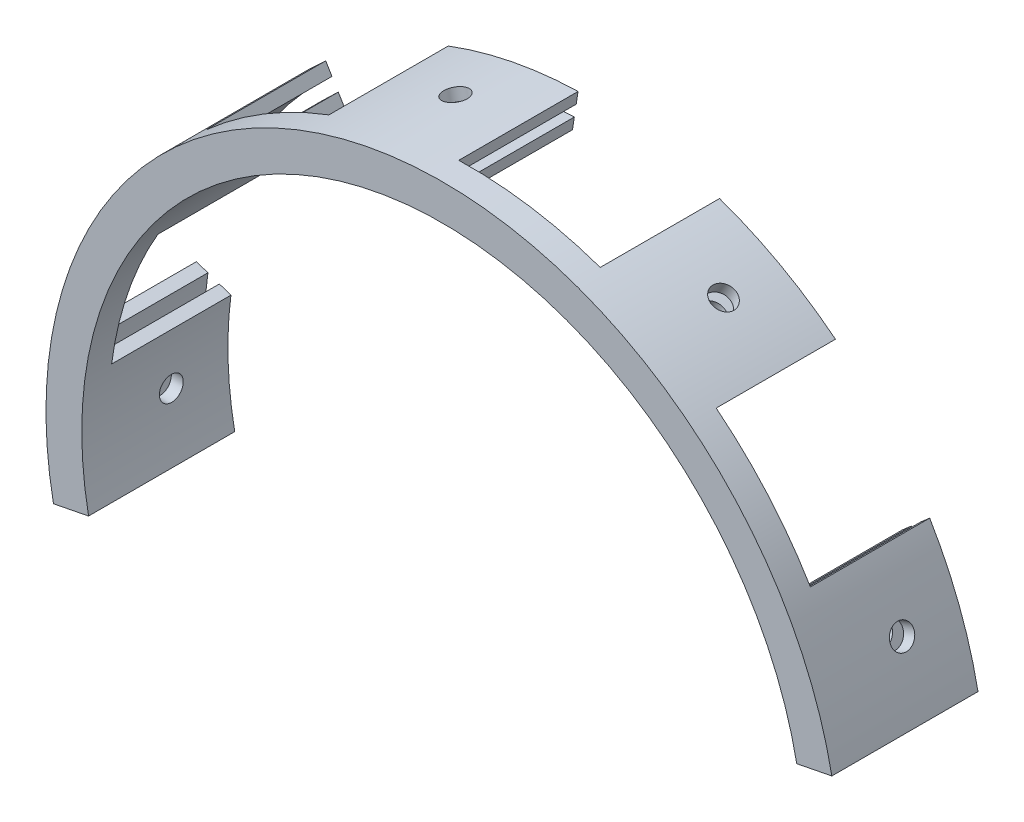
SolidWorks part; units mm, degrees
ref_plane "Front Plane" through (0, 0, 0) normal (0, 0, 1) x (1, 0, 0)
ref_plane "Top Plane" through (0, 0, 0) normal (0, 1, 0) x (1, 0, 0)
ref_plane "Right Plane" through (0, 0, 0) normal (1, 0, 0) x (0, 0, -1)
sketch "Sketch1" plane through (0, 0, 0) normal (0, 0, 1) x (1, 0, 0)
  line L2 (63.2821, 12.4748) -> (65.2444, 12.8616)
  line L3 (61.3199, 12.088) -> (59.3577, 11.7012)
  line L4 (-63.2821, -12.4748) -> (-61.3199, -12.088)
  line L5 (61.3199, 12.088) -> (63.2821, 12.4748)
  line L8 (-61.3199, -12.088) -> (-59.3577, -11.7012)
  line L9 (-63.2821, -12.4748) -> (-65.2444, -12.8616)
  arc A2 (65.2444, 12.8616) -> (-65.2444, -12.8616) centre (0, 0) ccw
  arc A3 (59.3577, 11.7012) -> (-59.3577, -11.7012) centre (0, 0) ccw
  arc A4 (63.2821, 12.4748) -> (-63.2821, -12.4748) centre (0, 0) ccw
  arc A5 (61.3199, 12.088) -> (-61.3199, -12.088) centre (0, 0) ccw
  arc A6 (63.2821, 12.4748) -> (-63.2821, -12.4748) centre (0, 0) ccw
  arc A7 (61.3199, 12.088) -> (-61.3199, -12.088) centre (0, 0) ccw
  dimension "D1" = 0
  dimension "D2" = 2
  dimension "D3" = 2
extrude "Boss-Extrude1" add sketch "Sketch1" against normal blind 22
sketch "Sketch2" plane through (0, 0, 0) normal (0, 0, 1) x (1, 0, 0)
  line L0 (-65.2444, -12.8616) -> (-59.3577, -11.7012)
  line L1 (59.3577, 11.7012) -> (65.2444, 12.8616)
  arc A0 (65.2444, 12.8616) -> (-65.2444, -12.8616) centre (0, 0) ccw construction
  arc A1 (59.3577, 11.7012) -> (-59.3577, -11.7012) centre (0, 0) ccw construction
  arc A2 (65.2444, 12.8616) -> (-65.2444, -12.8616) centre (0, 0) ccw
  arc A3 (59.3577, 11.7012) -> (-59.3577, -11.7012) centre (0, 0) ccw
extrude "Boss-Extrude2" add sketch "Sketch2" along normal blind 2.5
sketch "Sketch4" plane through (0, 0, 0) normal (0.1934, -0.9811, 0) x (0.9811, 0.1934, 0)
  line L0 (0, 0) -> (0, 49.5442) construction
  line L1 (0, 0) -> (24.6684, 0) construction
sketch "Sketch6" plane through (0, 0, 2.5) normal (0, 0, 1) x (1, 0, 0)
  line L0 (0, 0) -> (56.424, 21.8308) construction
  line L1 (0, 0) -> (59.3577, 11.7012) construction
  line L2 (0, 0) -> (45.5547, 39.8124) construction
  arc A0 (59.3577, 11.7012) -> (-59.3577, -11.7012) centre (0, 0) ccw construction
  point P6 (0, 0)
  dimension "D1" = 10
  dimension "D2" = 20
ref_plane "Plane3" through (56.424, 21.8308, 2.5) normal (0.9326, 0.3608, 0) x (0, 0, -1)
sketch "Sketch7" plane through (56.424, 21.8308, 2.5) normal (0.9326, 0.3608, 0) x (0, 0, -1)
  line L2 (0, 66.5) -> (0, -11.5476) construction
  line L3 (2.5, 0) -> (-47.0442, 0) construction
  line L4 (15, 0) -> (-47.0442, 0) construction
  circle A0 centre (15, 0) radius 2
  point P2 (13.5134, 0)
  point P5 (0, 0)
  point P8 (0, 0)
  point P9 (14.698, 0)
  dimension "D1" = 4
  dimension "D2" = 15
extrude "Cut-Extrude2" cut sketch "Sketch7" against normal through all both and the other way through all contours A0
pattern_circular "CirPattern1" count 5 every 40 about axis through (0, 0, 0) along (0, 0, 1) of "Cut-Extrude2"
ref_plane "Plane4" through (45.5547, 39.8124, 2.5) normal (0.753, 0.6581, 0) x (0, 0, -1)
sketch "Sketch8" plane through (45.5547, 39.8124, 2.5) normal (0.753, 0.6581, 0) x (0, 0, -1)
  line L0 (24.5, -33.25) -> (24.5, 66.5) construction
  line L1 (24.5, 12) -> (4.5, 12)
  line L2 (24.5, 12) -> (24.5, -12)
  line L3 (24.5, -12) -> (4.5, -12)
  line L4 (4.5, 12) -> (4.5, -12)
  line L5 (0, 0) -> (24.5, 0) construction
  line L6 (2.5, 0) -> (-47.0442, 0) construction
  line L7 (0, 0) -> (0, -30.25) construction
  line L8 (2.5, -31.25) -> (2.5, 62.5) construction
  dimension "D1" = 12
  dimension "D2" = 2
extrude "Cut-Extrude3" cut sketch "Sketch8" against normal through all both and the other way through all
pattern_circular "CirPattern2" count 4 every 40 about axis through (0, 0, 0) along (0, 0, 1) of "Cut-Extrude3"
